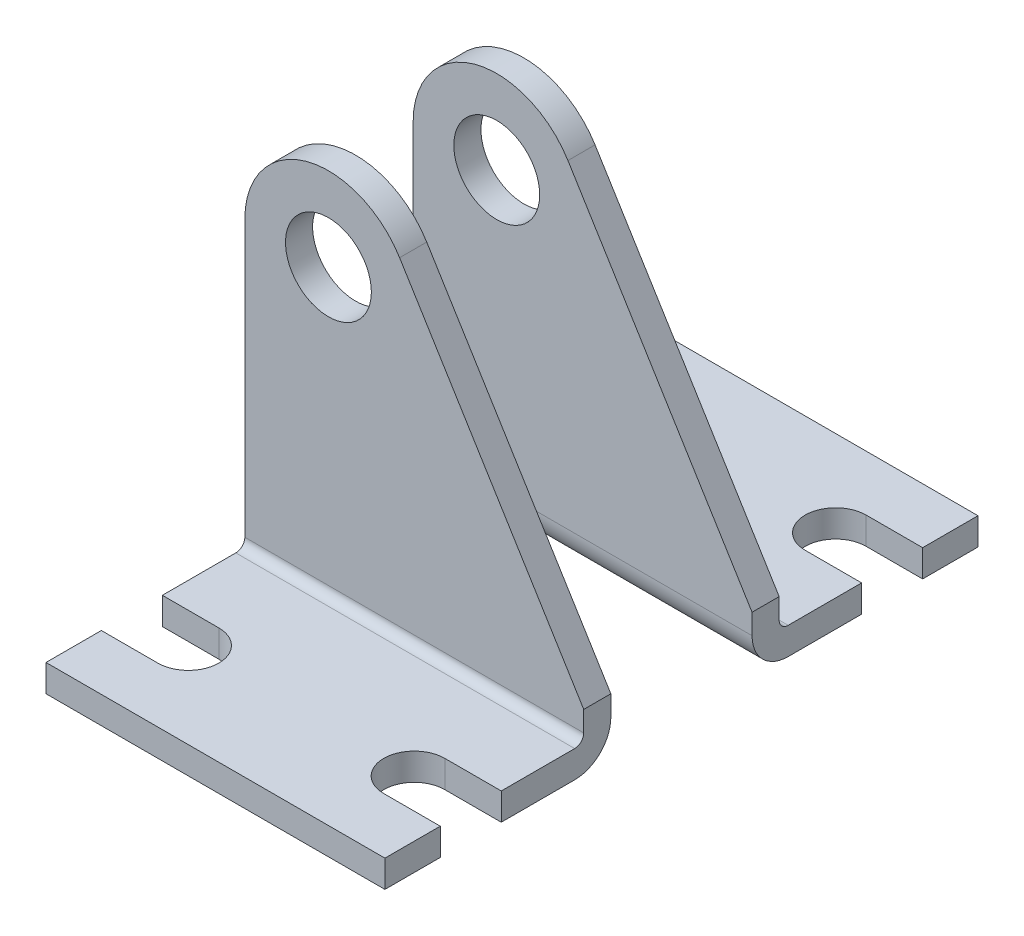
SolidWorks part; units mm, degrees
material "Galvanized Steel"
ref_plane "Front Plane" through (0, 0, 0) normal (0, 0, 1) x (1, 0, 0)
ref_plane "Top Plane" through (0, 0, 0) normal (0, 1, 0) x (1, 0, 0)
ref_plane "Right Plane" through (0, 0, 0) normal (1, 0, 0) x (0, 0, -1)
sketch "Sketch1" plane through (0, 0, 0) normal (0, 0, 1) x (1, 0, 0)
  line L0 (-9.398, 0) -> (-9.398, -35.052)
  line L1 (-9.398, -35.052) -> (28.702, -35.052)
  line L2 (28.702, -35.052) -> (28.702, -28.702)
  line L3 (28.702, -28.702) -> (8.0034, 4.9262)
  line L4 (-9.398, -32.004) -> (28.702, -32.004) construction
  circle A0 centre (0, 0) radius 4.826
  arc A1 (8.0034, 4.9262) -> (-9.398, 0) centre (0, 0) ccw
  point P9 (0, 4.826)
  dimension "Hole" = 9.652
  dimension "Height" = 44.45
  dimension "Vert Height" = 6.35
  dimension "Width" = 38.1
  dimension "Thickness" = 3.048
  dimension "Vert Hole" = 35.052
sketch "Sketch2" plane through (0, 0, 0) normal (0, 1, 0) x (1, 0, 0)
  line L0 (-9.398, -15.748) -> (28.702, -15.748) construction
  line L1 (-9.398, -25.4) -> (28.702, -25.4)
  line L2 (-9.398, -25.4) -> (-9.398, 0)
  line L3 (-9.398, 0) -> (28.702, 0)
  line L4 (28.702, -25.4) -> (28.702, 0)
  line L5 (-3.048, -19.177) -> (-9.398, -19.177)
  line L6 (-3.048, -12.319) -> (-9.398, -12.319)
  line L7 (22.352, -12.319) -> (28.702, -12.319)
  line L8 (22.352, -19.177) -> (28.702, -19.177)
  arc A0 (-3.048, -19.177) -> (-3.048, -12.319) centre (-3.048, -15.748) ccw
  arc A1 (22.352, -12.319) -> (22.352, -19.177) centre (22.352, -15.748) ccw
  dimension "Depth" = 25.4
  dimension "Hole Offset" = 15.748
  dimension "Hole Location" = 25.4
  dimension "Hole Size" = 6.858
sketch "Sketch3" plane through (0, 0, 0) normal (0, 0, 1) x (1, 0, 0)
  line L0 (-9.398, 0) -> (-9.398, -35.052) construction
  line L1 (28.702, -28.702) -> (8.0034, 4.9262) construction
  line L2 (28.702, -35.052) -> (28.702, -28.702) construction
  line L3 (-9.398, -35.052) -> (28.702, -35.052) construction
  line L4 (-9.398, 0) -> (-9.398, -35.052)
  line L5 (28.702, -28.702) -> (8.0034, 4.9262)
  line L6 (28.702, -35.052) -> (28.702, -28.702)
  line L7 (-9.398, -35.052) -> (28.702, -35.052)
  arc A0 (8.0034, 4.9262) -> (-9.398, 0) centre (0, 0) ccw construction
  circle A1 centre (0, 0) radius 4.826 construction
  arc A2 (8.0034, 4.9262) -> (-9.398, 0) centre (0, 0) ccw
  circle A3 centre (0, 0) radius 4.826
extrude "Boss-Extrude1" add sketch "Sketch3" along normal blind 3.048
sketch "Sketch4" plane through (0, 0, 3.048) normal (0, 0, 1) x (1, 0, 0)
  line L1 (-9.398, -35.052) -> (28.702, -35.052)
  line L2 (-9.398, -35.052) -> (-9.398, -32.004)
  line L3 (-9.398, -32.004) -> (28.702, -32.004)
  line L4 (28.702, -35.052) -> (28.702, -32.004)
extrude "Boss-Extrude2" add sketch "Sketch4" along normal up to vertex (22.352 mm away) up to point (-9.398, 0, 25.4)
sketch "Sketch5" plane through (0, -32.004, 0) normal (0, 1, 0) x (1, 0, 0)
  line L0 (-3.048, -19.177) -> (-9.398, -19.177) construction
  line L1 (-3.048, -12.319) -> (-9.398, -12.319) construction
  line L2 (22.352, -12.319) -> (28.702, -12.319) construction
  line L3 (22.352, -19.177) -> (28.702, -19.177) construction
  line L4 (-3.048, -19.177) -> (-9.398, -19.177)
  line L5 (-3.048, -12.319) -> (-9.398, -12.319)
  line L6 (22.352, -12.319) -> (28.702, -12.319)
  line L7 (22.352, -19.177) -> (28.702, -19.177)
  line L8 (-9.398, -19.177) -> (-9.398, -12.319)
  line L9 (28.702, -19.177) -> (28.702, -12.319)
  arc A0 (-3.048, -19.177) -> (-3.048, -12.319) centre (-3.048, -15.748) ccw construction
  arc A1 (22.352, -12.319) -> (22.352, -19.177) centre (22.352, -15.748) ccw construction
  arc A2 (-3.048, -19.177) -> (-3.048, -12.319) centre (-3.048, -15.748) ccw
  arc A3 (22.352, -12.319) -> (22.352, -19.177) centre (22.352, -15.748) ccw
extrude "Cut-Extrude1" cut sketch "Sketch5" against normal through all
fillet "Fillet1" radius 1.016 1 edges
fillet "Fillet2" radius 4.064 1 edges at (9.652, -35.052, 0)
ref_plane "Plane1" through (0, 0, -7.9375) normal (0, 0, 1) x (1, 0, 0)
mirror "Mirror2" about plane through (0, 0, -7.9375) normal (0, 0, 1) of bodies 103
sketch "Sketch8" plane through (0, 0, -18.923) normal (0, 0, -1) x (-1, 0, 0)
  line L0 (0, 4.826) -> (0, -4.826) construction
  circle A0 centre (0, 0) radius 4.826 construction
equation "\"D1@Boss-Extrude1\" = \"Thickness@Sketch1\""
equation "\"D1@Fillet1\" = \"Thickness@Sketch1\"/3"
equation "\"D1@Fillet2\" = \"Thickness@Sketch1\"+\"D1@Fillet1\""
